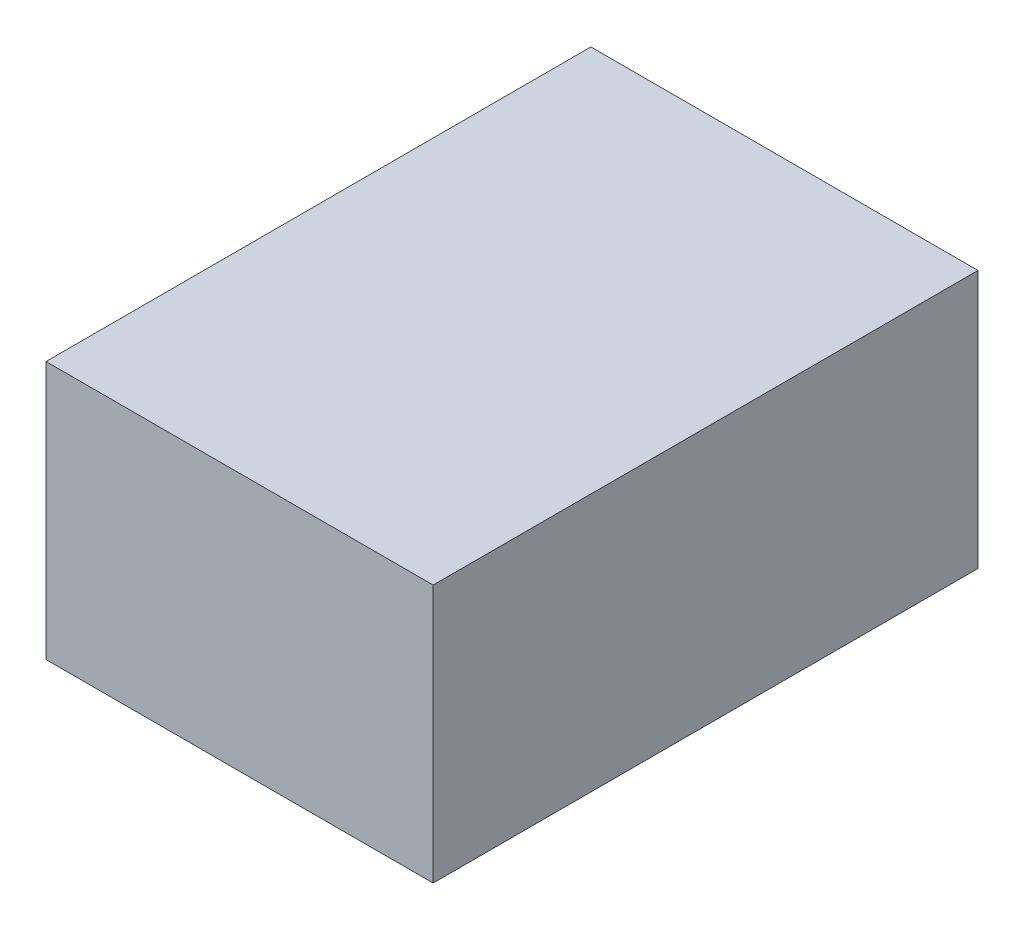
SolidWorks part; units mm, degrees
ref_plane "Front Plane" through (0, 0, 0) normal (0, 0, 1) x (1, 0, 0)
ref_plane "Top Plane" through (0, 0, 0) normal (0, 1, 0) x (1, 0, 0)
ref_plane "Right Plane" through (0, 0, 0) normal (1, 0, 0) x (0, 0, -1)
sketch "Sketch1" plane through (0, 0, 0) normal (0, 1, 0) x (1, 0, 0)
  line L1 (0, 0) -> (27, 0)
  line L2 (0, 0) -> (0, 38)
  line L3 (0, 38) -> (27, 38)
  line L4 (27, 0) -> (27, 38)
  dimension "D1" = 38
  dimension "D2" = 27
extrude "Boss-Extrude1" add sketch "Sketch1" along normal blind 18
